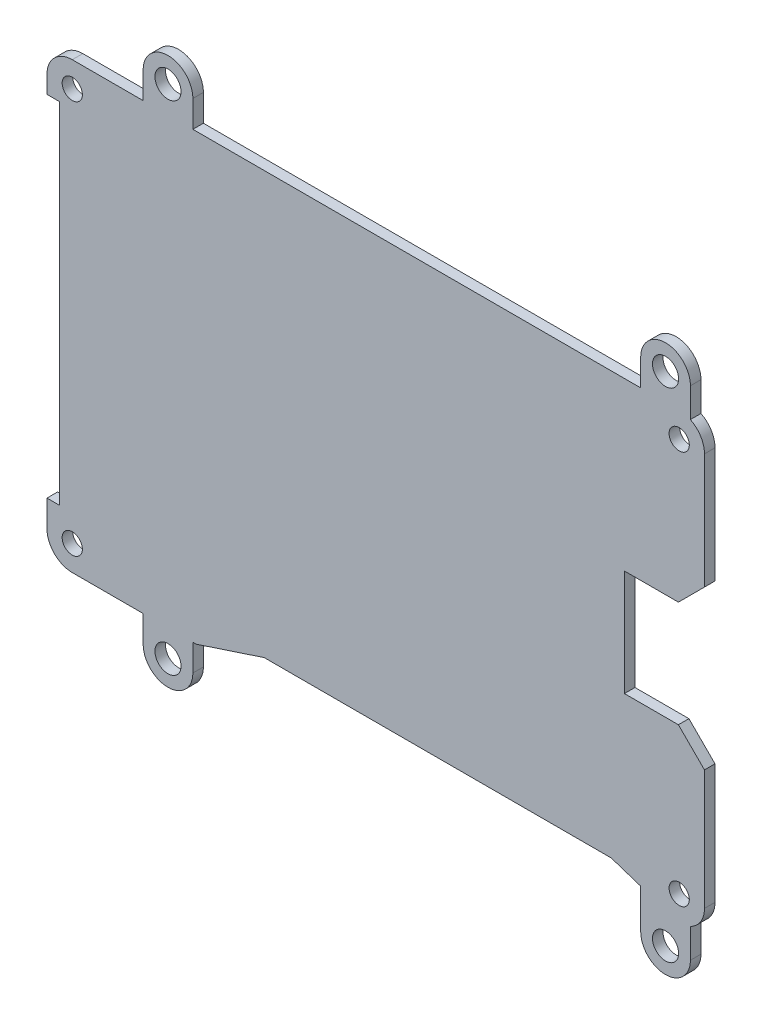
SolidWorks part; units mm, degrees
ref_plane "Front Plane" through (0, 0, 0) normal (0, 0, 1) x (1, 0, 0)
ref_plane "Top Plane" through (0, 0, 0) normal (0, 1, 0) x (1, 0, 0)
ref_plane "Right Plane" through (0, 0, 0) normal (1, 0, 0) x (0, 0, -1)
sketch "Sketch1" plane through (0, 0, 0) normal (0, 0, 1) x (1, 0, 0)
  line L5 (-301.9473, 132.8157) -> (-301.9473, 150.9704) construction
  line L6 (-305.7573, 154.7804) -> (-397.2471, 154.7804) construction
  line L7 (-401.0571, 150.9566) -> (-401.0571, 148.341) construction
  line L8 (-401.0571, 148.341) -> (-399.1521, 148.341) construction
  line L9 (-399.1521, 148.341) -> (-399.1521, 95.6449) construction
  line L10 (-399.1521, 95.6449) -> (-401.0571, 95.6449) construction
  line L11 (-401.0571, 95.6449) -> (-401.0571, 91.6593) construction
  line L12 (-397.2472, 87.8217) -> (-378.5565, 87.8217) construction
  line L13 (-378.5565, 87.8217) -> (-368.3165, 91.1883) construction
  line L14 (-368.3165, 91.1883) -> (-315.9973, 91.1883) construction
  line L15 (-315.9973, 91.1883) -> (-305.7573, 87.8217) construction
  line L16 (-301.9473, 91.6317) -> (-301.9473, 111.7465) construction
  line L17 (-301.9473, 133.5777) -> (-305.878, 129.6471)
  line L18 (-305.878, 129.6471) -> (-314.0123, 129.6471)
  line L19 (-314.0123, 129.6471) -> (-314.0123, 113.6451)
  line L20 (-314.0123, 113.6451) -> (-305.8779, 113.6451)
  line L21 (-305.8779, 113.6451) -> (-301.9473, 109.7145)
  line L22 (-301.9473, 133.5777) -> (-301.9473, 150.9704)
  line L23 (-305.7573, 154.7804) -> (-397.2471, 154.7804)
  line L24 (-401.0571, 150.9566) -> (-401.0571, 148.341)
  line L25 (-401.0571, 148.341) -> (-399.1521, 148.341)
  line L26 (-399.1521, 148.341) -> (-399.1521, 95.6449)
  line L27 (-399.1521, 95.6449) -> (-401.0571, 95.6449)
  line L28 (-401.0571, 95.6449) -> (-401.0571, 91.6593)
  line L29 (-397.2472, 87.8217) -> (-378.5565, 87.8217)
  line L30 (-378.5565, 87.8217) -> (-368.3165, 91.1883)
  line L31 (-368.3165, 91.1883) -> (-315.9973, 91.1883)
  line L32 (-315.9973, 91.1883) -> (-305.7573, 87.8217)
  line L33 (-301.9473, 91.6317) -> (-301.9473, 109.7145)
  circle A4 centre (-305.7573, 150.9704) radius 1.524
  circle A5 centre (-397.2471, 150.9704) radius 1.524
  circle A6 centre (-397.2472, 91.6317) radius 1.524
  circle A7 centre (-305.7573, 91.6317) radius 1.524
  arc A8 (-301.9473, 150.9704) -> (-305.7573, 154.7804) centre (-305.7573, 150.9704) ccw construction
  arc A9 (-397.2471, 154.7804) -> (-401.0571, 150.9566) centre (-397.2471, 150.9704) ccw construction
  arc A10 (-401.0571, 91.6593) -> (-397.2472, 87.8217) centre (-397.2472, 91.6317) ccw construction
  arc A11 (-305.7573, 87.8217) -> (-301.9473, 91.6317) centre (-305.7573, 91.6317) ccw construction
  arc A12 (-301.9473, 150.9704) -> (-305.7573, 154.7804) centre (-305.7573, 150.9704) ccw
  arc A13 (-397.2471, 154.7804) -> (-401.0571, 150.9566) centre (-397.2471, 150.9704) ccw
  arc A14 (-401.0571, 91.6593) -> (-397.2472, 87.8217) centre (-397.2472, 91.6317) ccw
  arc A15 (-305.7573, 87.8217) -> (-301.9473, 91.6317) centre (-305.7573, 91.6317) ccw
  dimension "D7" = 3.048
  dimension "D1" = 17.3927
  dimension "D2" = 3.9306
  dimension "D3" = 16.002
  dimension "D4" = 3.9307
  dimension "D5" = 8.1343
  dimension "D6" = 3.9307
extrude "Boss-Extrude1" add sketch "Sketch1" along normal blind 1.5875
sketch "Sketch2" plane through (0, 0, 1.5875) normal (0, 0, 1) x (1, 0, 0)
  line L0 (-351.5022, 121.301) -> (-351.5022, 159.401) construction
  line L1 (-301.9473, 150.9704) -> (-301.9473, 91.6317) construction
  line L2 (-401.0571, 121.301) -> (-301.9473, 121.301) construction
  line L3 (-351.5022, 83.201) -> (-351.5022, 159.401) construction
  line L4 (-361.0272, 83.201) -> (-361.0272, 159.401)
  line L5 (-341.9772, 83.201) -> (-341.9772, 159.401)
  line L6 (-361.0272, 154.7804) -> (-341.9772, 154.7804)
  line L7 (-305.7573, 154.7804) -> (-397.2471, 154.7804) construction
  line L8 (-361.0272, 91.6317) -> (-341.9772, 91.6317)
  circle A0 centre (-351.5022, 159.401) radius 3.175
  arc A1 (-361.0272, 83.201) -> (-341.9772, 83.201) centre (-351.5022, 83.201) ccw
  arc A2 (-341.9772, 159.401) -> (-361.0272, 159.401) centre (-351.5022, 159.401) ccw
  circle A3 centre (-351.5022, 83.201) radius 3.175
  point P13 (-351.5022, 121.301)
  line M11 (-305.7573, 154.7804) -> (-397.2471, 154.7804)
  line M21 (-368.3165, 91.1883) -> (-315.9973, 91.1883)
  dimension "D1" = 6.35
  dimension "D2" = 38.1
  dimension "D3" = 19.05
extrude "Boss-Extrude2" [suppressed] add sketch "Sketch2" against normal blind 1.5875 contours L5 A2 L4 A0 M11 | L4 A1 L5 A3 M21
sketch "Sketch6" plane through (0, 0, 1.5875) normal (0, 0, 1) x (1, 0, 0)
  line L0 (-386.6812, 159.8604) -> (-386.6812, 154.7804)
  line L1 (-305.7573, 154.7804) -> (-397.2471, 154.7804) construction
  line L2 (-379.8232, 159.8604) -> (-379.8232, 154.7804)
  line L3 (-379.8232, 154.7804) -> (-386.6812, 154.7804)
  line L4 (-316.3232, 159.8604) -> (-316.3232, 154.7804)
  line L5 (-316.3232, 154.7804) -> (-323.1812, 154.7804)
  line L6 (-323.1812, 154.7804) -> (-323.1812, 159.8604)
  line L7 (-383.2522, 159.8604) -> (-319.7522, 159.8604) construction
  line L8 (-351.5022, 159.8604) -> (-351.5022, 154.7804) construction
  line L10 (-351.5022, 154.7804) -> (-351.5022, 91.1883) construction
  line L11 (-368.3165, 91.1883) -> (-315.9973, 91.1883) construction
  line L12 (-361.2812, 83.5683) -> (-361.2812, 91.1883)
  line L13 (-361.2812, 91.1883) -> (-354.4232, 91.1883)
  line L14 (-354.4232, 91.1883) -> (-354.4232, 83.5683)
  circle A0 centre (-383.2522, 159.8604) radius 1.7843
  circle A1 centre (-319.7522, 159.8604) radius 1.7843
  circle A2 centre (-383.2522, 159.8604) radius 3.429
  circle A3 centre (-319.7522, 159.8604) radius 3.429
  circle A4 centre (-357.8522, 83.5683) radius 1.7145
  circle A5 centre (-357.8522, 83.5683) radius 3.429
  line M7 (-305.7573, 154.7804) -> (-397.2471, 154.7804)
  line M17 (-368.3165, 91.1883) -> (-315.9973, 91.1883)
  dimension "D2" = 6.858
  dimension "D3" = 3.5687
  dimension "D4" = 5.08
  dimension "D5" = 6.858
  dimension "D6" = 3.429
  dimension "D7" = 7.62
  dimension "D1" = 63.5
  dimension "D8" = 38.1
extrude "Boss-Extrude4" [suppressed] add sketch "Sketch6" against normal up to vertex contours A2 A0 | A2 L0 L2 M7 | A3 L6 L4 M7 | A3 A1 | A5 A4 | A5 L14 L12 M17
sketch "Sketch7" [suppressed] plane through (0, 0, 1.5875) normal (0, 0, 1) x (1, 0, 0)
  line L0 (-351.5022, 154.7804) -> (-351.5022, 91.1883) construction
  line L1 (-305.7573, 154.7804) -> (-397.2471, 154.7804) construction
  line L2 (-368.3165, 91.1883) -> (-315.9973, 91.1883) construction
  line L3 (-383.2522, 159.8604) -> (-319.7522, 159.8604) construction
  line L4 (-351.5022, 159.8604) -> (-351.5022, 154.7804) construction
  line L5 (-386.6812, 159.8604) -> (-386.6812, 154.7804)
  line L6 (-386.6812, 154.7804) -> (-379.8232, 154.7804)
  line L7 (-379.8232, 154.7804) -> (-379.8232, 159.8604)
  line L8 (-323.1812, 159.8604) -> (-323.1812, 154.7804)
  line L9 (-323.1812, 154.7804) -> (-316.3232, 154.7804)
  line L10 (-316.3232, 154.7804) -> (-316.3232, 159.8604)
  line L11 (-354.9312, 83.6604) -> (-354.9312, 91.1883)
  line L12 (-354.9312, 91.1883) -> (-348.0732, 91.1883)
  line L13 (-348.0732, 91.1883) -> (-348.0732, 83.6604)
  circle A0 centre (-383.2522, 159.8604) radius 1.7843
  circle A1 centre (-319.7522, 159.8604) radius 1.7843
  circle A2 centre (-383.2522, 159.8604) radius 3.429
  circle A3 centre (-319.7522, 159.8604) radius 3.429
  circle A4 centre (-351.5022, 83.6604) radius 1.7843
  circle A5 centre (-351.5022, 83.6604) radius 3.429
  line M5 (-305.7573, 154.7804) -> (-397.2471, 154.7804)
  line M15 (-368.3165, 91.1883) -> (-315.9973, 91.1883)
  dimension "D1" = 3.5687
  dimension "D3" = 6.858
  dimension "D2" = 63.5
  dimension "D4" = 5.08
  dimension "D5" = 76.2
extrude "Boss-Extrude5" [suppressed] add sketch "Sketch7" against normal up to vertex contours A2 L5 L7 M5 | A2 A0 | A3 L8 L10 M5 | A3 A1 | A5 A4 | A5 L13 L11 M15
sketch "Sketch8" plane through (0, 0, 1.5875) normal (0, 0, 1) x (1, 0, 0)
  line L0 (-397.2471, 154.7804) -> (-397.2472, 87.8217) construction
  line L1 (-382.8146, 158.8011) -> (-307.8146, 158.801) construction
  line L2 (-382.8146, 158.8011) -> (-382.8146, 83.8011) construction
  line L3 (-382.8146, 83.8011) -> (-307.8146, 83.801) construction
  line L4 (-307.8146, 158.801) -> (-307.8146, 83.801) construction
  line L5 (-397.2472, 121.301) -> (-382.8146, 121.301) construction
  line L6 (-386.5611, 158.8011) -> (-386.5611, 154.7804)
  line L7 (-305.7573, 154.7804) -> (-397.2471, 154.7804) construction
  line L8 (-379.0681, 158.8011) -> (-379.0681, 154.7804)
  line L9 (-311.5611, 158.801) -> (-311.5611, 154.7804)
  line L10 (-304.0681, 158.801) -> (-304.0681, 154.3855)
  line L11 (-311.5611, 83.8011) -> (-311.5611, 89.7298)
  line L12 (-315.9973, 91.1883) -> (-305.7573, 87.8217) construction
  line L13 (-304.0681, 83.8011) -> (-304.0681, 88.2166)
  line L14 (-379.0681, 83.801) -> (-379.0681, 87.8217)
  line L15 (-397.2472, 87.8217) -> (-378.5565, 87.8217) construction
  line L16 (-386.5611, 83.801) -> (-386.5611, 87.8217)
  circle A0 centre (-382.8146, 158.8011) radius 1.9685
  circle A1 centre (-307.8146, 158.801) radius 1.9685
  circle A2 centre (-307.8146, 83.801) radius 1.9685
  circle A3 centre (-382.8146, 83.8011) radius 1.9685
  circle A4 centre (-382.8146, 158.8011) radius 3.7465
  circle A5 centre (-307.8146, 158.801) radius 3.7465
  circle A6 centre (-307.8146, 83.801) radius 3.7465
  circle A7 centre (-382.8146, 83.8011) radius 3.7465
  arc A8 (-301.9473, 150.9704) -> (-305.7573, 154.7804) centre (-305.7573, 150.9704) ccw construction
  arc A9 (-305.7573, 87.8217) -> (-301.9473, 91.6317) centre (-305.7573, 91.6317) ccw construction
  arc M4 (-301.9473, 150.9704) -> (-305.7573, 154.7804) centre (-305.7573, 150.9704) ccw
  line M5 (-305.7573, 154.7804) -> (-397.2471, 154.7804)
  line M13 (-397.2472, 87.8217) -> (-378.5565, 87.8217)
  line M16 (-315.9973, 91.1883) -> (-305.7573, 87.8217)
  arc M17 (-305.7573, 87.8217) -> (-301.9473, 91.6317) centre (-305.7573, 91.6317) ccw
  dimension "D3" = 3.937
  dimension "D1" = 75
  dimension "D2" = 75
  dimension "D4" = 14.4325
  dimension "D5" = 1.778
extrude "Boss-Extrude6" add sketch "Sketch8" against normal up to vertex (1.5875 mm away) contours A4 L6 L8 M5 | A4 A0 | A5 L9 L10 M5 M4 | A5 A1 | A6 L13 L11 M17 M16 | A6 A2 | A7 L14 L16 M13 | A7 A3 up to point (-378.5565, 87.8217, 0)
